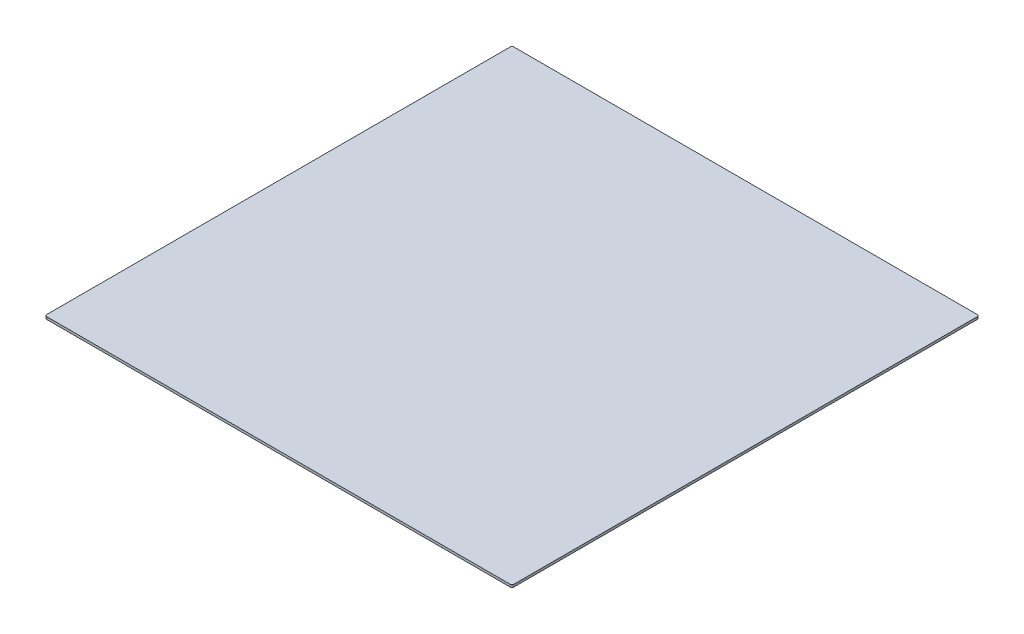
SolidWorks part; units mm, degrees
ref_plane "Front Plane" through (0, 0, 0) normal (0, 0, 1) x (1, 0, 0)
ref_plane "Top Plane" through (0, 0, 0) normal (0, 1, 0) x (1, 0, 0)
ref_plane "Right Plane" through (0, 0, 0) normal (1, 0, 0) x (0, 0, -1)
sketch "Sketch1" plane through (0, 0, 0) normal (0, 1, 0) x (1, 0, 0)
  line L1 (-1219.2, 1219.2) -> (1219.2, 1219.2)
  line L2 (-1219.2, 1219.2) -> (-1219.2, -1219.2)
  line L3 (-1219.2, -1219.2) -> (1219.2, -1219.2)
  line L4 (1219.2, 1219.2) -> (1219.2, -1219.2)
  line L5 (-1219.2, 1219.2) -> (1219.2, -1219.2) construction
  line L6 (-1219.2, -1219.2) -> (1219.2, 1219.2) construction
  point P0 (0, 0)
  dimension "D1" = 2438.4
extrude "Boss-Extrude1" add sketch "Sketch1" along normal blind 12.7
fillet "Fillet1" radius 10 4 edges at (-1219.2, 6.35, -1219.2) (1219.2, 6.35, -1219.2) (-1219.2, 6.35, 1219.2) (1219.2, 6.35, 1219.2)
